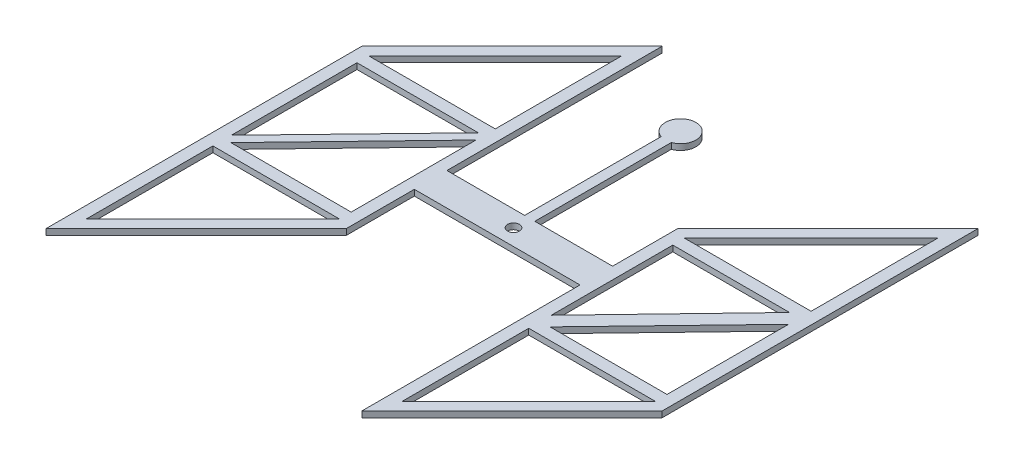
SolidWorks part; units mm, degrees
material "Cedar"
ref_plane "Front Plane" through (0, 0, 0) normal (0, 0, 1) x (1, 0, 0)
ref_plane "Top Plane" through (0, 0, 0) normal (0, 1, 0) x (1, 0, 0)
ref_plane "Right Plane" through (0, 0, 0) normal (1, 0, 0) x (0, 0, -1)
sketch "Sketch1" plane through (0, 0, 0) normal (0, 1, 0) x (1, 0, 0)
  line L0 (-203.2043, 9.4874) -> (-203.2048, -9.5206)
  line L1 (-177.8048, -34.9206) -> (177.7952, -34.9206)
  line L2 (499.9952, 496.8299) -> (499.9952, -503.1701) construction
  line L8 (499.9952, -503.1701) -> (-500.0048, -503.1701) construction
  line L9 (499.9952, 496.8299) -> (-500.0048, 496.8299) construction
  line L17 (-500.0048, 496.8299) -> (-500.0048, -503.1701) construction
  line L19 (-177.8043, 34.8874) -> (177.7957, 34.8874)
  line L22 (-177.8043, 34.8874) -> (-177.8043, 496.8299)
  line L23 (-177.8043, 496.8299) -> (-500.0048, 174.6294)
  line L24 (-500.0048, 174.6294) -> (-500.0048, -503.1701)
  line L25 (-500.0048, -503.1701) -> (-177.8048, -180.9701)
  line L26 (-177.8048, -180.9701) -> (-177.8048, -34.9206)
  line L28 (177.7952, -34.9206) -> (177.7952, -503.1701)
  line L29 (177.7952, -503.1701) -> (499.9952, -180.9701)
  line L30 (499.9952, -180.9701) -> (499.9952, 496.8299)
  line L31 (499.9952, 496.8299) -> (177.7957, 174.6304)
  line L32 (177.7957, 174.6304) -> (177.7957, 34.8874)
  line L34 (-203.2043, 9.4874) -> (-203.2043, 435.5089)
  line L35 (-203.2043, 435.5089) -> (-474.6048, 164.1084)
  line L36 (-474.6048, 164.1084) -> (-474.6048, -441.8491)
  line L37 (-474.6048, -441.8491) -> (-203.2048, -170.4491)
  line L38 (-203.2048, -170.4491) -> (-203.2048, -9.5206)
  line L50 (-0.0043, 34.8874) -> (-0.0043, -34.9206) construction
  line L52 (-474.6048, 164.1084) -> (-203.2043, 164.1084)
  line L55 (-203.2043, 164.1084) -> (-203.2043, 138.7084)
  line L56 (-203.2043, 138.7084) -> (-474.6048, 138.7084)
  line L57 (-203.2048, -145.0491) -> (-203.2048, -170.4491)
  line L58 (-203.2048, -170.4491) -> (-474.6048, -170.4491)
  line L59 (-203.2048, -145.0491) -> (-474.6048, -145.0491)
  line L61 (-203.2043, 138.7084) -> (-474.6048, -145.0491) construction
  line L68 (-203.2043, 435.5089) -> (-177.8043, 496.8299) construction
  line L69 (474.5952, 9.4874) -> (474.5947, -9.5206)
  line L82 (474.5952, 9.4874) -> (474.5952, 435.5089)
  line L83 (474.5952, 435.5089) -> (203.1947, 164.1084)
  line L84 (203.1947, 164.1084) -> (203.1947, -441.8491)
  line L85 (203.1947, -441.8491) -> (474.5947, -170.4491)
  line L86 (474.5947, -170.4491) -> (474.5947, -9.5206)
  line L87 (203.1947, 164.1084) -> (474.5952, 164.1084)
  line L88 (474.5952, 138.7084) -> (203.1947, 138.7084)
  line L89 (474.5947, -170.4491) -> (203.1947, -170.4491)
  line L90 (474.5947, -145.0491) -> (203.1947, -145.0491)
  line L92 (474.5952, 138.7084) -> (203.1947, -145.0491) construction
  line L96 (474.5952, 435.5089) -> (499.9952, 496.8299) construction
  line L97 (-10.9507, 34.8874) -> (-10.9507, 330.2914)
  line L98 (10.942, 34.8874) -> (10.942, 330.2914)
  line L99 (-10.9507, 34.8874) -> (10.942, 34.8874)
  line L100 (-10.9507, 330.2914) -> (10.942, 330.2914)
  line L101 (-214.241, 138.7084) -> (-474.6048, -130.8289)
  line L102 (-461.4544, -145.0491) -> (-203.2043, 122.9073)
  line L103 (453.6454, 138.7084) -> (203.1947, -122.1493)
  line L104 (474.5952, 115.7214) -> (223.4978, -145.0491)
  circle A0 centre (0, 358.6651) radius 32.7844
  circle A4 centre (0, 0) radius 12.7
extrude "Boss-Extrude1" add sketch "Sketch1" along normal blind 12.7
